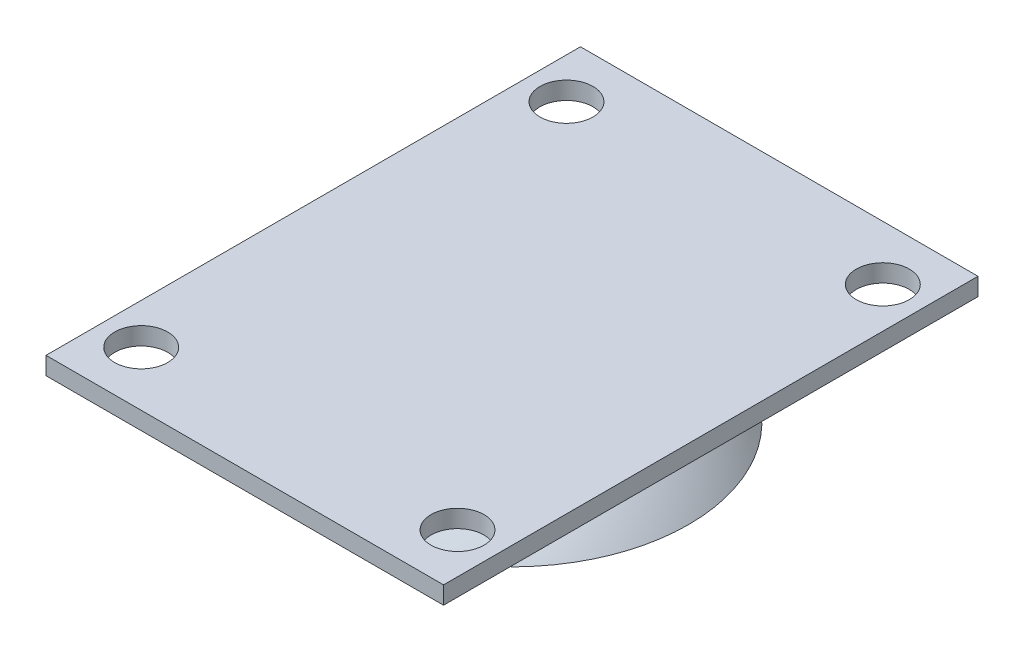
SolidWorks part; units mm, degrees
material "Chromium Copper, UNS C18200"
ref_plane "Front Plane" through (0, 0, 0) normal (0, 0, 1) x (1, 0, 0)
ref_plane "Top Plane" through (0, 0, 0) normal (0, 1, 0) x (1, 0, 0)
ref_plane "Right Plane" through (0, 0, 0) normal (1, 0, 0) x (0, 0, -1)
sketch "Sketch1" plane through (0, 0, 0) normal (0, 1, 0) x (1, 0, 0)
  line L0 (0, 37.0869) -> (0, -44.714) construction
  line L1 (-22.5, 30.25) -> (22.5, 30.25)
  line L2 (-22.5, 30.25) -> (-22.5, -30.25)
  line L3 (-22.5, -30.25) -> (22.5, -30.25)
  line L4 (22.5, 30.25) -> (22.5, -30.25)
  line L5 (-22.5, 30.25) -> (22.5, -30.25) construction
  line L6 (-22.5, -30.25) -> (22.5, 30.25) construction
  line L7 (28.9831, 0) -> (-36.8008, 0) construction
  circle A0 centre (17.9044, 24.0714) radius 3
  circle A1 centre (-17.9044, 24.0714) radius 3
  circle A2 centre (17.9044, -24.0714) radius 3
  circle A3 centre (-17.9044, -24.0714) radius 3
  point P0 (0, 0)
  dimension "D3" = 6
  dimension "D1" = 45
  dimension "D2" = 60.5
  dimension "D4" = 30
extrude "Boss-Extrude1" add sketch "Sketch1" along normal blind 2
sketch "Sketch2" plane through (0, 0, 0) normal (0, 0, 1) x (1, 0, 0)
  line L0 (0, 10.006) -> (0, -2.02) construction
  line L1 (0, 0) -> (0, -2.02)
  line L2 (20, -8.4681) -> (17.1604, -8.4681)
  line L3 (0, -2.9806) -> (0, -16.3725) construction
  line L4 (1.9993, -2.0726) -> (1.9993, -2.0726)
  line L5 (15.679, -7.1244) -> (15.679, -7.1244)
  line L6 (0, -2.02) -> (1.9993, -2.0726)
  line L7 (15.679, -7.1244) -> (17.1604, -8.4681)
  spline S0 degree 2 poles (0, 0) (12.4384, -0.0796) (20, -8.4681) knots 0 0 0 1 1 1
  spline S1 degree 1 poles (1.9993, -2.0726) (15.679, -7.1244) knots 0 0 1 1 construction
  spline S2 degree 3 poles (1.9993, -2.0726) (2.666, -2.1173) (4.014, -2.2516) (6.5495, -2.6834) (9.5254, -3.5338) (12.7654, -5.0356) (14.7494, -6.3804) (15.679, -7.1244) knots 0.087231 0.087231 0.087231 0.087231 0.177417 0.267603 0.447975 0.628347 0.808719 0.808719 0.808719 0.808719
  dimension "D1" = 20
  dimension "D2" = 2
revolve "Revolve1" add sketch "Sketch2" angle 360 about L0
